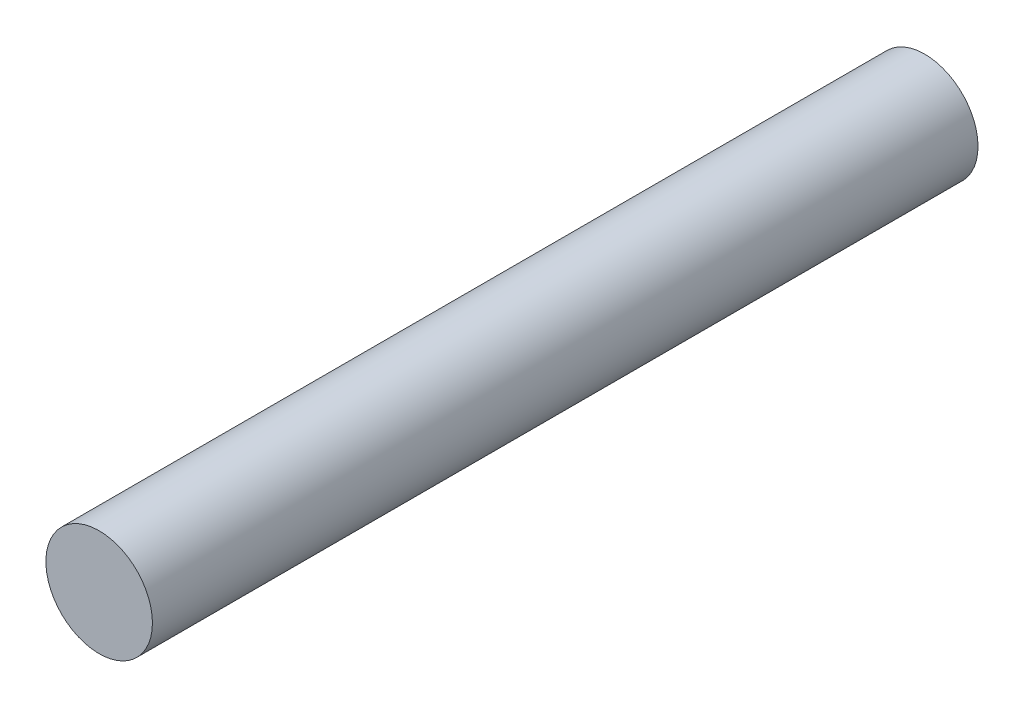
SolidWorks part; units mm, degrees
ref_plane "前视基准面" through (0, 0, 0) normal (0, 0, 1) x (1, 0, 0)
ref_plane "上视基准面" through (0, 0, 0) normal (0, 1, 0) x (1, 0, 0)
ref_plane "右视基准面" through (0, 0, 0) normal (1, 0, 0) x (0, 0, -1)
sketch "草图1" plane through (0, 0, 0) normal (0, 0, 1) x (1, 0, 0)
  circle A0 centre (0, 0) radius 4
extrude "凸台-拉伸1" add sketch "草图1" along normal blind 62
